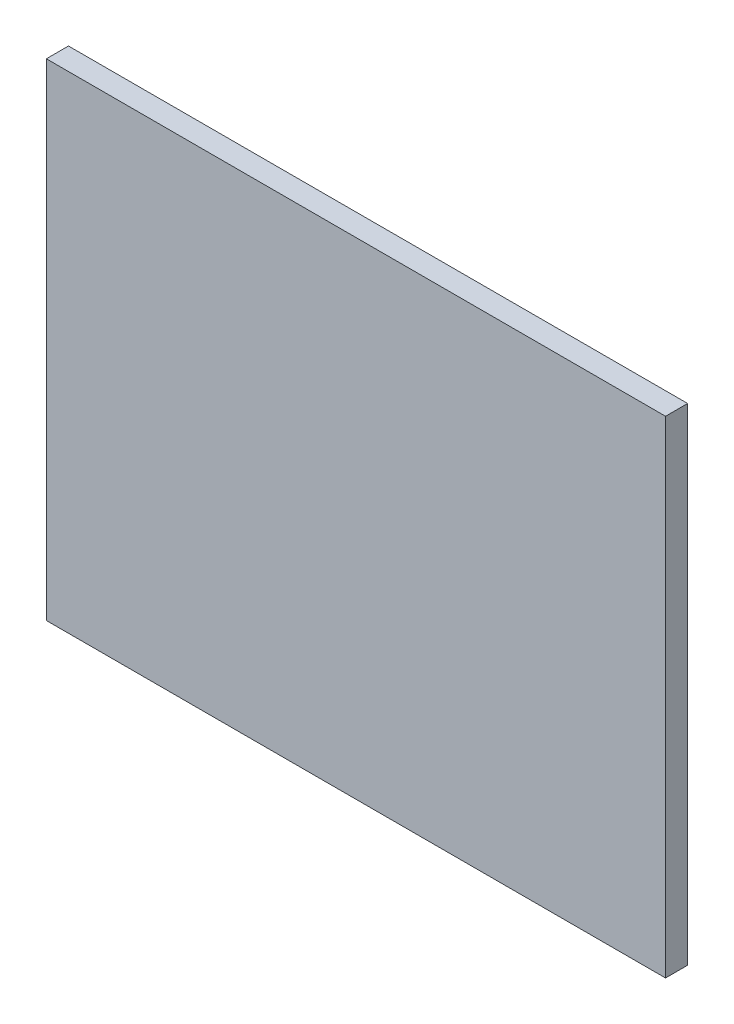
SolidWorks part; units mm, degrees
ref_plane "Front Plane" through (0, 0, 0) normal (0, 0, 1) x (1, 0, 0)
ref_plane "Top Plane" through (0, 0, 0) normal (0, 1, 0) x (1, 0, 0)
ref_plane "Right Plane" through (0, 0, 0) normal (1, 0, 0) x (0, 0, -1)
sketch "Sketch1" plane through (0, 0, 0) normal (0, 0, 1) x (1, 0, 0)
  line L1 (-115.5015, 97.9635) -> (164.4985, 97.9635)
  line L2 (-115.5015, 97.9635) -> (-115.5015, -122.0365)
  line L3 (-115.5015, -122.0365) -> (164.4985, -122.0365)
  line L4 (164.4985, 97.9635) -> (164.4985, -122.0365)
  dimension "D1" = 220
  dimension "D2" = 280
extrude "Boss-Extrude1" add sketch "Sketch1" along normal blind 10 contours L2 L1 L4 L3
